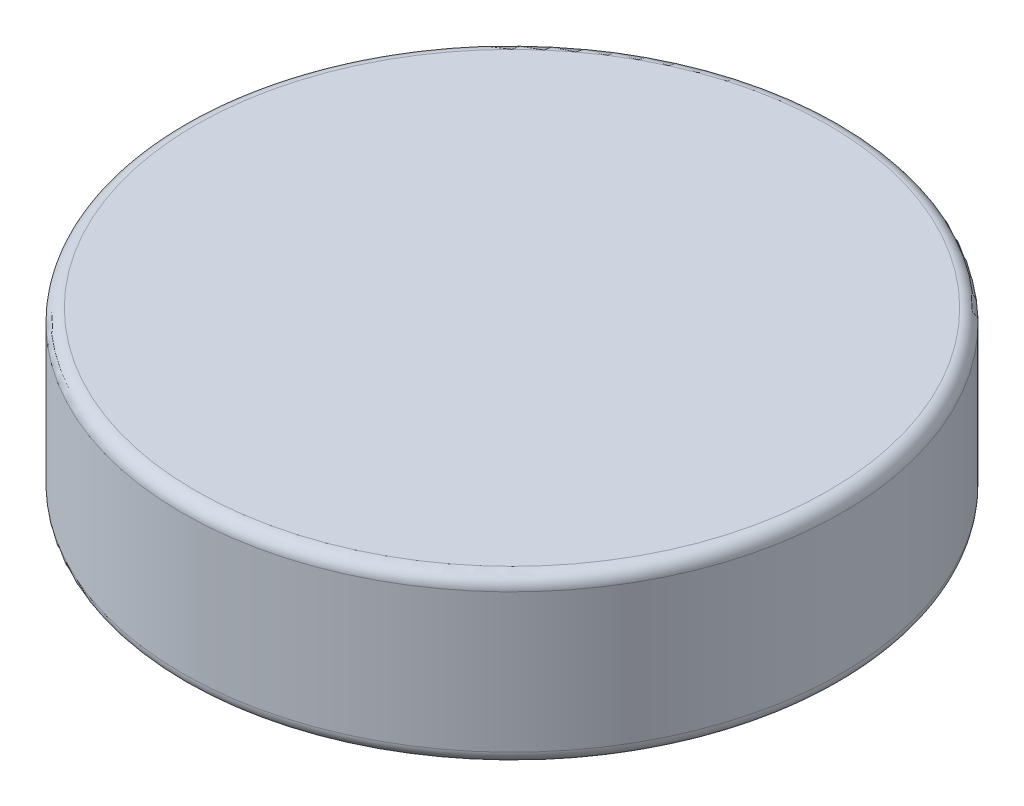
SolidWorks part; units mm, degrees
material "Neodymium"
ref_plane "Front Plane" through (0, 0, 0) normal (0, 0, 1) x (1, 0, 0)
ref_plane "Top Plane" through (0, 0, 0) normal (0, 1, 0) x (1, 0, 0)
ref_plane "Right Plane" through (0, 0, 0) normal (1, 0, 0) x (0, 0, -1)
sketch "Sketch1" plane through (0, 0, 0) normal (0, 1, 0) x (1, 0, 0)
  circle A0 centre (0, 0) radius 12.7
  dimension "D1" = 25.4
extrude "Boss-Extrude1" add sketch "Sketch1" along normal mid plane 6.35
fillet "Fillet1" radius 0.5 2 edges at (0, -3.175, 12.7) (0, 3.175, 12.7)
